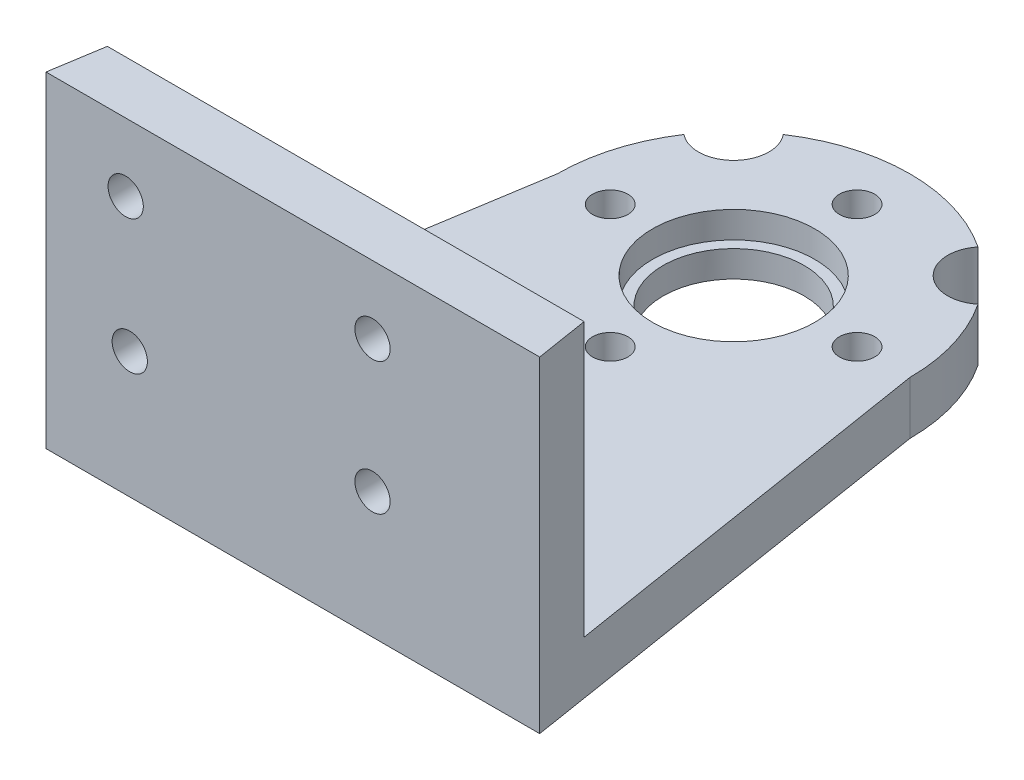
SolidWorks part; units mm, degrees
material "Custom Plastic"
ref_plane "Front Plane" through (0, 0, 0) normal (0, 0, 1) x (1, 0, 0)
ref_plane "Top Plane" through (0, 0, 0) normal (0, 1, 0) x (1, 0, 0)
ref_plane "Right Plane" through (0, 0, 0) normal (1, 0, 0) x (0, 0, -1)
sketch "Sketch1" plane through (0, 0, 0) normal (0, 1, 0) x (1, 0, 0)
  line L0 (-10, 0) -> (-14, -25)
  line L1 (10, 0) -> (14, -25)
  line L2 (0, 17.2103) -> (0, -39.4896) construction
  line L3 (-14, -25) -> (14, -25)
  arc A0 (-10, 0) -> (10, 0) centre (0, 0) cw
  dimension "D1" = 10
  dimension "D2" = 25
  dimension "D3" = 14
extrude "Boss-Extrude1" add sketch "Sketch1" along normal blind 3
sketch "Sketch2" plane through (0, 3, 0) normal (0, 1, 0) x (1, 0, 0)
  line L0 (-21.4034, 0) -> (30.5216, 0) construction
  circle A0 centre (0, 0) radius 4
  dimension "D1" = 8
extrude "Cut-Extrude1" cut sketch "Sketch2" against normal blind 13
sketch "Sketch3" plane through (0, 3, 0) normal (0, 1, 0) x (1, 0, 0)
  line L0 (0, 14.8087) -> (0, -39.0944) construction
  line L1 (-14, -25) -> (14, -25) construction
  line L2 (-10, 0) -> (0, 0) construction
  line L3 (-13.04, -19) -> (0, -19) construction
  line L4 (-10, 0) -> (-14, -25) construction
  line L5 (14, -25) -> (10, 0) construction
  circle A0 centre (-6.52, -19) radius 1
  circle A1 centre (6.52, -19) radius 1
  circle A2 centre (0, -19) radius 1
  point P3 (-6.52, -19)
  point P11 (-13.04, -19)
  point P12 (13.0353, -18.9708)
  point P18 (0, -19)
  dimension "D3" = 2
  dimension "D2" = 2
  dimension "D1" = 6
extrude "Cut-Extrude2" cut sketch "Sketch3" against normal blind 13
sketch "Sketch4" plane through (0, 3, 0) normal (0, 1, 0) x (1, 0, 0)
  line L0 (0, 11.5358) -> (0, -14.2328) construction
  circle A0 centre (0, -7) radius 1
  circle A1 centre (-7, 0) radius 1
  circle A2 centre (0, 7) radius 1
  circle A3 centre (7, 0) radius 1
  point P0 (0, -7)
  point P15 (0, 0)
  dimension "D2" = 2
  dimension "D1" = 7
  dimension "D3" = 4
extrude "Cut-Extrude3" cut sketch "Sketch4" against normal up to vertex (3 mm away) up to point (0, 0, 0)
sketch "Sketch5" plane through (0, 3, 0) normal (0, 1, 0) x (1, 0, 0)
  line L0 (-13.52, -22) -> (13.52, -22)
  line L1 (-10, 0) -> (-14, -25) construction
  line L2 (14, -25) -> (10, 0) construction
  line L3 (-13.52, -22) -> (-14, -25)
  line L4 (-14, -25) -> (14, -25)
  line L5 (14, -25) -> (13.52, -22)
  dimension "D1" = 3
extrude "Boss-Extrude2" add sketch "Sketch5" along normal blind 15.5
sketch "Sketch6" plane through (0, 3, 0) normal (0, 1, 0) x (1, 0, 0)
  circle A0 centre (0, 0) radius 4.6
  dimension "D1" = 9.2
extrude "Cut-Extrude4" cut sketch "Sketch6" against normal blind 1.5
sketch "Sketch7" plane through (0, 3, 0) normal (0, 1, 0) x (1, 0, 0)
  line L0 (0, 12.0905) -> (0, -12.7025) construction
  line L1 (-13.0501, 13.0501) -> (0, 0) construction
  circle A0 centre (-7.0711, 7.0711) radius 2
  arc A1 (10, 0) -> (-10, 0) centre (0, 0) ccw construction
  circle A2 centre (7.0711, 7.0711) radius 2
  dimension "D1" = 4
extrude "Cut-Extrude5" cut sketch "Sketch7" against normal blind 10
sketch "Sketch8" plane through (0, 0, 22) normal (0, 0, -1) x (-1, 0, 0)
  circle A0 centre (-4.5188, 7.1518) radius 1 construction
  circle A1 centre (-4.5188, 14.6518) radius 1 construction
  circle A2 centre (9.4812, 14.6518) radius 1 construction
  circle A3 centre (9.2488, 7.1518) radius 1 construction
  circle A4 centre (-4.5188, 7.1518) radius 1
  circle A5 centre (-4.5188, 14.6518) radius 1
  circle A6 centre (9.4812, 14.6518) radius 1
  circle A7 centre (9.2488, 7.1518) radius 1
extrude "Cut-Extrude6" cut sketch "Sketch8" against normal blind 10
